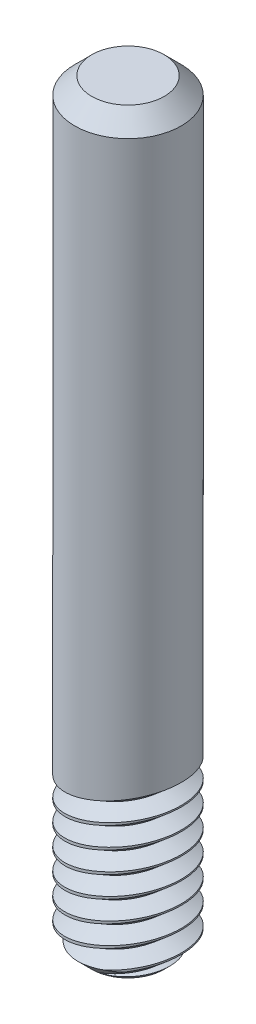
SolidWorks part; units mm, degrees
material "6061 Alloy"
ref_plane "Front" through (0, 0, 0) normal (0, 0, 1) x (1, 0, 0)
ref_plane "Top" through (0, 0, 0) normal (0, 1, 0) x (1, 0, 0)
ref_plane "Right" through (0, 0, 0) normal (1, 0, 0) x (0, 0, -1)
sketch "Sketch1" plane through (0, 0, 0) normal (0, 1, 0) x (1, 0, 0)
  circle A0 centre (0, 0) radius 1.5875
  dimension "D1" = 3.175
extrude "Boss-Extrude1" add sketch "Sketch1" along normal blind 22.5425
chamfer "Chamfer1" distance 0.508 angle 45 2 edges at (0, 22.5425, 1.5875) (0, 0, 1.5875)
sketch "Sketch2" plane through (0, 0, 0) normal (0, 0, 1) x (1, 0, 0)
  line L0 (0, 0) -> (0.7213, -3.7432) construction
  line L1 (1.5875, 0.635) -> (1.0988, 0.2115)
  line L2 (1.5875, 0.508) -> (1.5875, 22.0345) construction
  line L3 (1.0988, 0.2115) -> (1.7099, 0)
  line L4 (1.5875, 0.635) -> (1.7099, 0)
  line L5 (1.5875, 0.635) -> (2.1543, 0.635) construction
  line L6 (1.7099, 0) -> (2.1997, 0) construction
  line L7 (0, 0) -> (0, -7.6509) construction
  line L8 (-2.9703, -0.5726) -> (4.4386, 0.8551) construction
  line L9 (1.0988, 0.2115) -> (-1.0988, 0.2115) construction
  line L10 (-1.0988, 0.2115) -> (-1.0988, -0.2119) construction
  line L11 (1.0988, 0.2115) -> (1.0988, 0.635) construction
  line L12 (1.0988, 0.635) -> (1.5875, 0.635) construction
  point P14 (0, 0.2115)
  dimension "D1" = 0.635
revolve "Cut-Revolve1" cut sketch "Sketch2" angle 360 about L0
pattern_linear "LPattern1" count 4 spacing 0.635 along (0, 1, 0) count 2 spacing 2.54 along (0, 1, 0) of "Cut-Revolve1"
